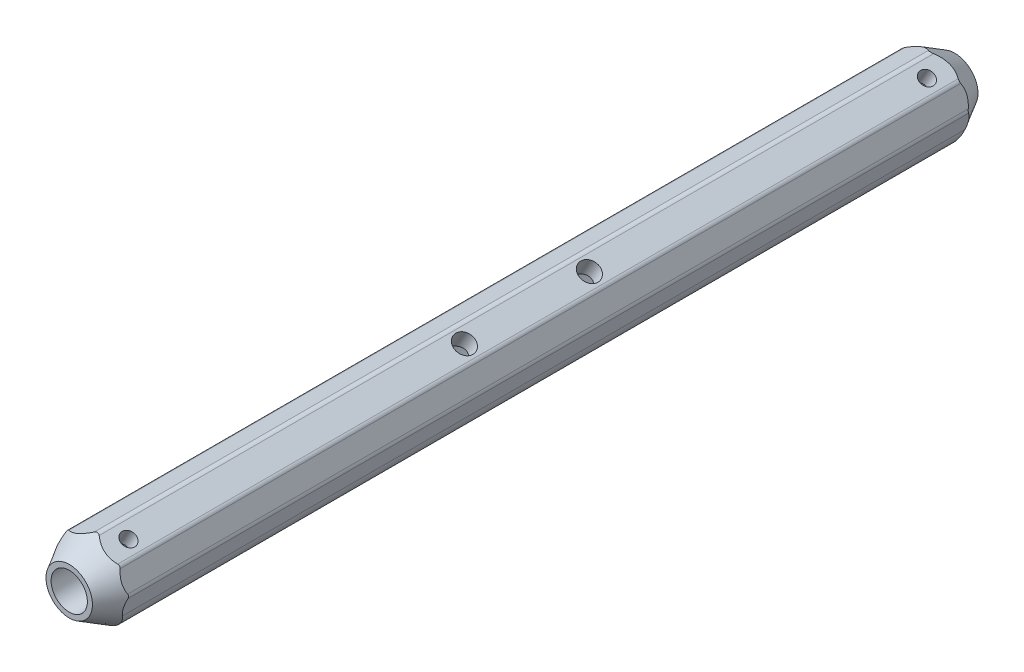
SolidWorks part; units mm, degrees
material "6061-T6 (SS)"
ref_plane "Front Plane" through (0, 0, 0) normal (0, 0, 1) x (1, 0, 0)
ref_plane "Top Plane" through (0, 0, 0) normal (0, 1, 0) x (1, 0, 0)
ref_plane "Right Plane" through (0, 0, 0) normal (1, 0, 0) x (0, 0, -1)
sketch "Sketch1" plane through (0, 0, 0) normal (0, 0, 1) x (1, 0, 0)
  line L1 (-7.627, -9.453) -> (-3.7427, -11.6955) construction
  line L4 (-9.519, 9.2593) -> (-11.8203, 0.6706) construction
  line L5 (-7.627, -9.453) -> (-3.7427, -11.6955)
  line L6 (0.6598, 13.4755) -> (-9.519, 9.2593) construction
  line L7 (9.5277, 8.3556) -> (0.6598, 13.4755) construction
  line L8 (12.6454, 0.8288) -> (9.5277, 8.3556) construction
  line L9 (10.9165, -5.6235) -> (12.6454, 0.8288) construction
  line L10 (-9.519, 9.2593) -> (-11.8203, 0.6706)
  line L11 (0.6598, 13.4755) -> (-9.519, 9.2593)
  line L12 (9.5277, 8.3556) -> (0.6598, 13.4755)
  line L13 (12.6454, 0.8288) -> (9.5277, 8.3556)
  line L14 (10.9165, -5.6235) -> (12.6454, 0.8288)
  arc A0 (-11.8203, 0.6706) -> (-7.627, -9.453) centre (-3.127, -1.6587) ccw construction
  arc A1 (-3.7427, -11.6955) -> (10.9165, -5.6235) centre (1.2573, -3.0353) ccw construction
  arc A2 (-11.8203, 0.6706) -> (-7.627, -9.453) centre (-3.127, -1.6587) ccw
  arc A3 (-3.7427, -11.6955) -> (10.9165, -5.6235) centre (1.2573, -3.0353) ccw
  circle A4 centre (0, 0) radius 6.25 construction
  circle A5 centre (0, 0) radius 6.25
extrude "Boss-Extrude1" add sketch "Sketch1" along normal mid plane 305
fillet "Fillet1" radius 2 4 edges at (12.6454, 0.8288, 0) (9.5277, 8.3556, 0) (0.6598, 13.4755, 0) (-9.519, 9.2593, 0)
sketch "Sketch2" plane through (0, 0, 0) normal (0, 1, 0) x (1, 0, 0)
  line L0 (0, 164.7848) -> (0, -151.0044) construction
  line L1 (-46.1187, 0) -> (117.6011, 0) construction
  line L2 (-0.2514, 152.5) -> (-8.6078, 152.5) construction
  line L5 (-8, 152.5) -> (-20, 152.5)
  line L6 (-8, 152.5) -> (-20, 131.7154)
  line L8 (-20, 152.5) -> (-20, 131.7154)
  line L9 (-9.7742, 152.5) -> (-11.8203, 152.5) construction
  line L10 (-8, -152.5) -> (-20, -152.5)
  line L11 (-8, -152.5) -> (-20, -131.7154)
  line L12 (-20, -152.5) -> (-20, -131.7154)
  point P17 (0, 152.5)
  point P18 (20, 0)
  point P22 (-20, 0)
  dimension "D1" = 8
  dimension "D2" = 60
  dimension "D3" = 12
revolve "Cut-Revolve2" cut sketch "Sketch2" angle 360 about L0
hole_wizard "M8 Tapped Hole1" positions "Sketch3" profile "Sketch4" tap size "M8" standard "ISO"
sketch "Sketch3" plane through (8, 13.8564, 0) normal (0.5, 0.866, 0) x (-0.866, 0.5, 0)
  line L0 (1, 21.5249) -> (1, -21.5249) construction
  line L2 (0, 0) -> (1, 0) construction
  point P1 (1, 21.5249)
  point P5 (1, -21.5249)
sketch "Sketch4" plane through (7.134, 14.3564, 21.5249) normal (0, 0, 1) x (-0.866, 0.5, 0)
  line L0 (0, 0) -> (0, 24.2929)
  line L1 (0, 24.2929) -> (3.4, 22.25)
  line L2 (3.4, 22.25) -> (3.4, 0)
  line L3 (3.4, 0) -> (0, 0)
  line L4 (0, 24.2929) -> (-3.4, 22.25) construction
  line L5 (0, -6.35) -> (0, 107.95) construction
  dimension "Tap Drill Dia." = 6.8
  dimension "Tap Drill Depth" = 22.25
  dimension "Drill Angle" = 118
hole_wizard "M8 Tapped Hole2" positions "Sketch6" profile "Sketch5" tap size "M8" standard "ISO"
sketch "Sketch6" plane through (-11.1962, 3, 0) normal (-0.9659, 0.2588, 0) x (0, 0, 1)
  line L2 (-152.5, 8) -> (-152.5, -8) construction
  line L3 (152.5, -8) -> (152.5, 8) construction
  point P0 (-123, 2)
  point P1 (123, 2)
  dimension "D1" = 29.5
  dimension "D2" = 29.5
  dimension "D3" = 2
sketch "Sketch5" plane through (-10.6785, 4.9319, -123) normal (0, 0, 1) x (-0.2588, -0.9659, 0)
  line L0 (0, 0) -> (0, 17.0429)
  line L1 (0, 17.0429) -> (3.4, 15)
  line L2 (3.4, 15) -> (3.4, 0)
  line L5 (3.4, 0) -> (0, 0)
  line L10 (0, 17.0429) -> (-3.4, 15) construction
  line L11 (0, -6.35) -> (0, 107.95) construction
  dimension "Tap Drill Dia." = 6.8
  dimension "Tap Drill Depth" = 15
  dimension "Drill Angle" = 118
cosmetic thread "Hole Thread3" parameters "D1"=11, "D2"=8
cosmetic thread "Hole Thread4" parameters "D1"=11, "D2"=8
hole_wizard "Ø3.0 (3) Diameter Hole1" positions "Sketch8" profile "Sketch7" hole size "Ø3.0" standard "Ansi Metric"
sketch "Sketch8" plane through (-11.1962, 3, 0) normal (-0.9659, 0.2588, 0) x (0, 0, 1)
  circle A1 centre (-123, 2) radius 8.3 construction
  circle A2 centre (123, 2) radius 8.3 construction
  point P0 (115.0855, -0.5)
  point P1 (-115.0855, -0.5)
  dimension "D1" = 16.6
  dimension "D2" = 2.5
sketch "Sketch7" plane through (-11.3256, 2.517, 115.0855) normal (0, 0, 1) x (-0.2588, -0.9659, 0)
  line L0 (0, 0) -> (0, 10.9013)
  line L1 (0, 10.9013) -> (1.5, 10)
  line L2 (1.5, 10) -> (1.5, 0)
  line L5 (1.5, 0) -> (0, 0)
  line L10 (0, 10.9013) -> (-1.5, 10) construction
  line L11 (0, -6.35) -> (0, 107.95) construction
  dimension "Hole Dia." = 3
  dimension "Hole Depth" = 10
  dimension "Drill Angle" = 118
hole_wizard "M6 Tapped Hole1" positions "Sketch10" profile "Sketch9" tap size "M6" standard "ISO"
sketch "Sketch10" plane through (6, 10.3923, 0) normal (0.5, 0.866, 0) x (0.866, -0.5, 0)
  line L0 (6.25, 152.5) -> (-6.25, 152.5) construction
  line L1 (-8, -152.5) -> (8, -152.5) construction
  line L2 (-12.6862, 143.8453) -> (-12.6862, -143.8453) construction
  point P0 (-0.6862, -137.5)
  point P2 (-0.6862, 137.5)
  dimension "D1" = 15
  dimension "D2" = 15
  dimension "D3" = 12
sketch "Sketch9" plane through (5.4057, 10.7354, 137.5) normal (0, 0, 1) x (-0.866, 0.5, 0)
  line L0 (0, 0) -> (0, 15.5022)
  line L1 (0, 15.5022) -> (2.5, 14)
  line L2 (2.5, 14) -> (2.5, 0)
  line L5 (2.5, 0) -> (0, 0)
  line L10 (0, 15.5022) -> (-2.5, 14) construction
  line L11 (0, -6.35) -> (0, 107.95) construction
  dimension "Tap Drill Dia." = 5
  dimension "Tap Drill Depth" = 14
  dimension "Drill Angle" = 118
cosmetic thread "Hole Thread6" parameters "D1"=6.2718, "D2"=6
cosmetic thread "Hole Thread7" parameters "D1"=6.2718, "D2"=6
